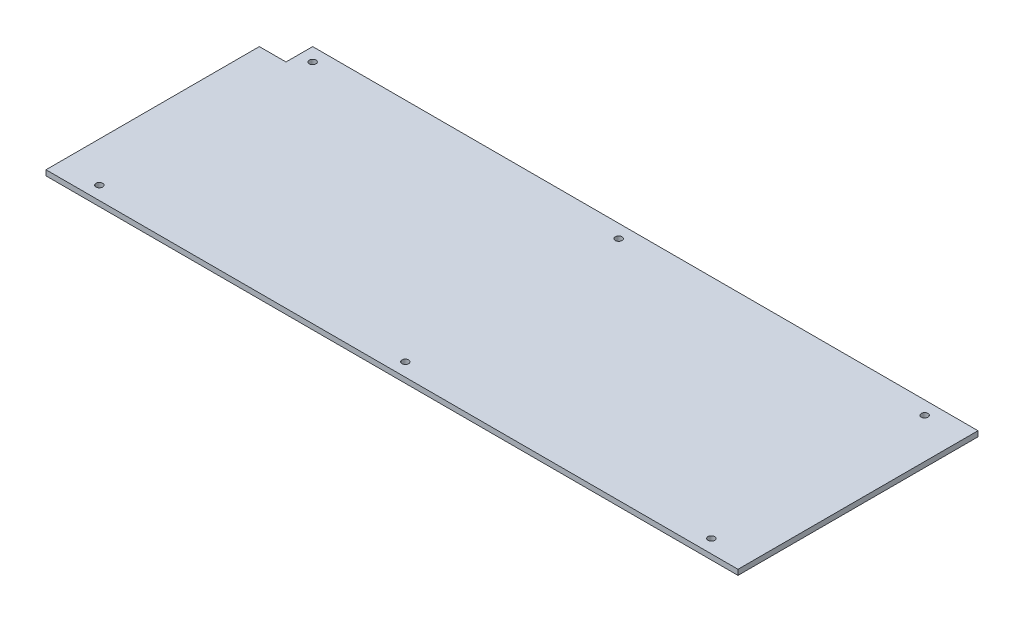
SolidWorks part; units mm, degrees
ref_plane "Front Plane" through (0, 0, 0) normal (0, 0, 1) x (1, 0, 0)
ref_plane "Top Plane" through (0, 0, 0) normal (0, 1, 0) x (1, 0, 0)
ref_plane "Right Plane" through (0, 0, 0) normal (1, 0, 0) x (0, 0, -1)
sketch "Sketch1" plane through (0, 0, 0) normal (0, 1, 0) x (1, 0, 0)
  line L0 (0, 90) -> (0, -90) construction
  line L1 (-259.5, -90) -> (259.5, -90)
  line L2 (-259.5, -90) -> (-259.5, 90) construction
  line L3 (-259.5, 90) -> (259.5, 90) construction
  line L4 (259.5, -90) -> (259.5, 90)
  line L5 (-259.5, -90) -> (259.5, 90) construction
  line L6 (-259.5, 90) -> (259.5, -90) construction
  line L7 (-259.5, 0) -> (259.5, 0) construction
  line L8 (259.5, 90) -> (-239.5, 90)
  line L9 (-259.5, 90) -> (-239.5, 90) construction
  line L10 (-259.5, 90) -> (-259.5, 70) construction
  line L11 (-259.5, 70) -> (-239.5, 70)
  line L12 (-239.5, 90) -> (-239.5, 70)
  line L19 (-259.5, 70) -> (-259.5, -90)
  circle A0 centre (-229.5, 80) radius 2.5
  circle A2 centre (229.5, 80) radius 2.5
  circle A3 centre (-229.5, -80) radius 2.5
  circle A5 centre (229.5, -80) radius 2.5
  circle A6 centre (0, 80) radius 2.5
  circle A7 centre (0, -80) radius 2.5
  point P0 (0, 0)
  dimension "D3" = 5
  dimension "D4" = 20
  dimension "D7" = 30
  dimension "D8" = 5
  dimension "D1" = 180
  dimension "D2" = 519
  dimension "D5" = 20
  dimension "D6" = 10
  dimension "D9" = 10
extrude "Boss-Extrude1" add sketch "Sketch1" along normal blind 4
